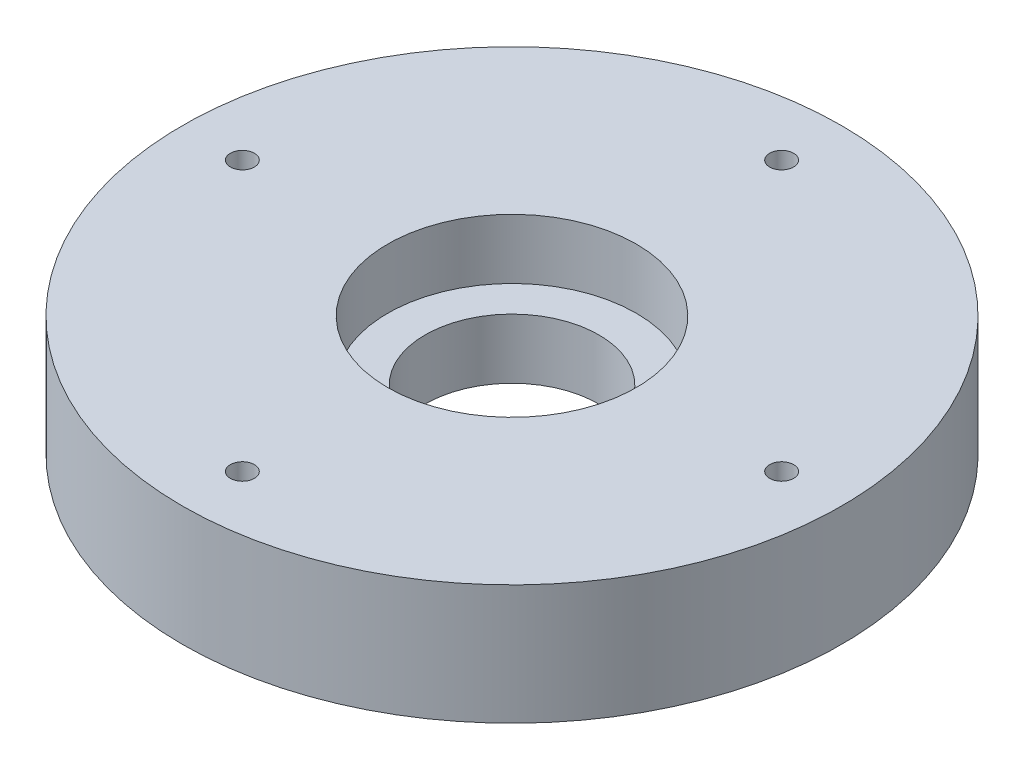
SolidWorks part; units mm, degrees
material "ABS"
ref_plane "Front Plane" through (0, 0, 0) normal (0, 0, 1) x (1, 0, 0)
ref_plane "Top Plane" through (0, 0, 0) normal (0, 1, 0) x (1, 0, 0)
ref_plane "Right Plane" through (0, 0, 0) normal (1, 0, 0) x (0, 0, -1)
sketch "Sketch1" plane through (0, 0, 0) normal (0, 1, 0) x (1, 0, 0)
  circle A0 centre (0, 0) radius 55
  circle A1 centre (0, 0) radius 14.5
  dimension "D1" = 110
  dimension "D2" = 29
extrude "Boss-Extrude1" add sketch "Sketch1" along normal blind 20
sketch "Sketch2" plane through (0, 20, 0) normal (0, 1, 0) x (1, 0, 0)
  circle A0 centre (0, 0) radius 20.75
  dimension "D1" = 41.5
extrude "Cut-Extrude1" cut sketch "Sketch2" against normal blind 10
sketch "Sketch4" plane through (0, 20, 0) normal (0, 1, 0) x (1, 0, 0)
  line L0 (0, 0) -> (42.5992, 0) construction
  line L1 (0, 0) -> (0, 40.5872) construction
  circle A0 centre (0, 45) radius 2
  circle A1 centre (45, 0) radius 2
  circle A2 centre (0, -45) radius 2
  circle A3 centre (-45, 0) radius 2
  point P15 (0, 0)
  dimension "D1" = 4
  dimension "D2" = 45
  dimension "D3" = 4
extrude "Cut-Extrude2" cut sketch "Sketch4" against normal blind 20
sketch "Sketch6" plane through (0, 0, 0) normal (0, -1, 0) x (1, 0, 0)
  circle A0 centre (0, 45) radius 5
  circle A1 centre (45, 0) radius 5
  circle A2 centre (0, -45) radius 5
  circle A3 centre (-45, 0) radius 5
  point P12 (0, 0)
  dimension "D1" = 10
  dimension "D2" = 4
extrude "Cut-Extrude3" cut sketch "Sketch6" against normal blind 5
